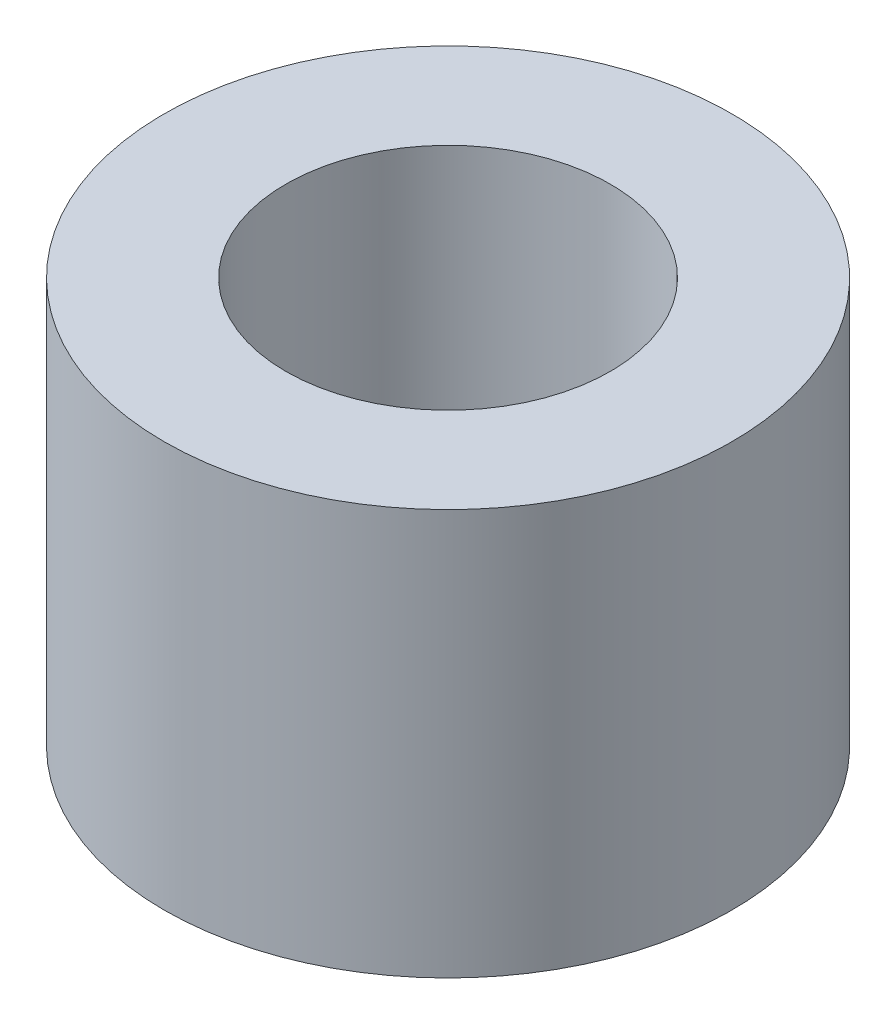
SolidWorks part; units mm, degrees
ref_plane "Front Plane" through (0, 0, 0) normal (0, 0, 1) x (1, 0, 0)
ref_plane "Top Plane" through (0, 0, 0) normal (0, 1, 0) x (1, 0, 0)
ref_plane "Right Plane" through (0, 0, 0) normal (1, 0, 0) x (0, 0, -1)
sketch "Sketch1" plane through (0, 0, 0) normal (0, 1, 0) x (1, 0, 0)
  circle A0 centre (-8.3136, 2.0784) radius 3.5
  circle A1 centre (-8.3136, 2.0784) radius 2
extrude "Boss-Extrude2" add sketch "Sketch1" along normal blind 5
